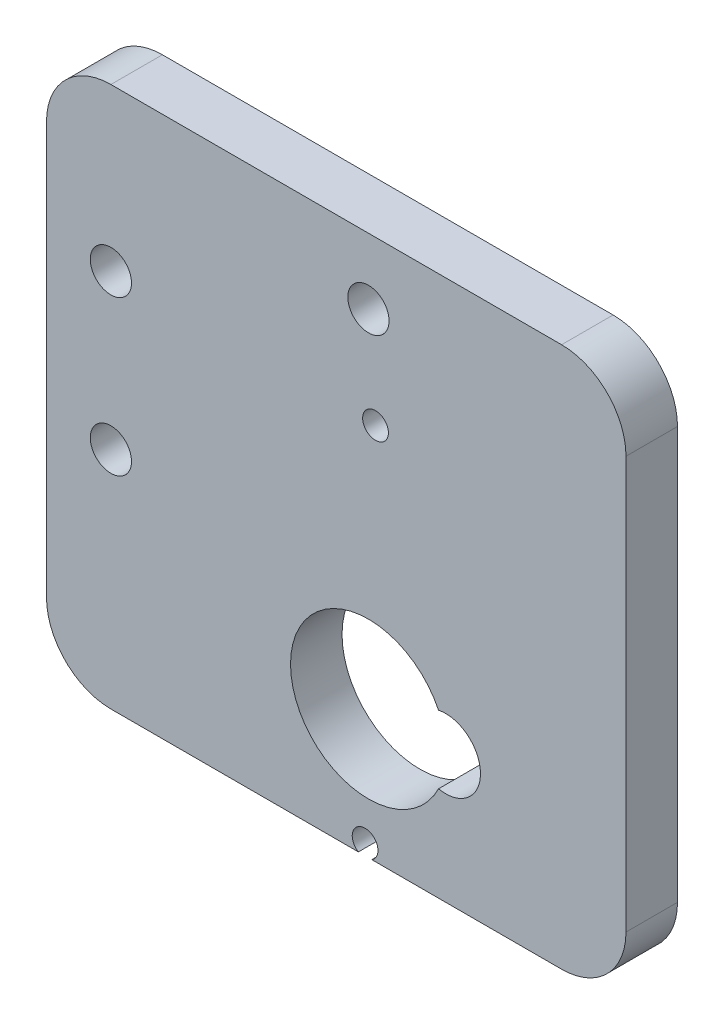
SolidWorks part; units mm, degrees
ref_plane "Front Plane" through (0, 0, 0) normal (0, 0, 1) x (1, 0, 0)
ref_plane "Top Plane" through (0, 0, 0) normal (0, 1, 0) x (1, 0, 0)
ref_plane "Right Plane" through (0, 0, 0) normal (1, 0, 0) x (0, 0, -1)
sketch "Sketch1" plane through (0, 0, 0) normal (0, 0, 1) x (1, 0, 0)
  line L0 (0, 0) -> (0, 26.9) construction
  line L1 (0, 13.45) -> (-20, 13.45) construction
  line L2 (-25, 32) -> (20, 32)
  line L3 (-25, 32) -> (-25, -10)
  line L4 (-25, -10) -> (20, -10)
  line L5 (20, 32) -> (20, -10)
  line L6 (-20, 19.45) -> (-20, 7.45) construction
  arc A0 (5.4427, 2.6419) -> (5.4427, -2.6419) centre (0, 0) ccw
  arc A1 (5.4427, -2.6419) -> (5.4427, 2.6419) centre (6, 0) ccw
  circle A2 centre (0, 26.9) radius 1.6
  circle A3 centre (-20, 19.45) radius 1.6
  circle A4 centre (-20, 7.45) radius 1.6
  arc A5 (0.3168, -9.963) -> (-0.8827, -9.9289) centre (-0.2602, -9.1463) ccw construction
  arc A6 (0.3168, -9.963) -> (-0.8827, -9.9289) centre (-0.2602, -9.1463) ccw
  arc A7 (0.3168, -9.963) -> (-0.8827, -9.9289) centre (-0.2602, -9.1463) cw
  arc A8 (-0.0268, 20.1589) -> (1.1727, 20.1248) centre (0.5502, 19.3422) ccw construction
  arc A9 (-0.0268, 20.1589) -> (1.1727, 20.1248) centre (0.5502, 19.3422) ccw
  arc A10 (-0.0268, 20.1589) -> (1.2511, 18.629) centre (0.5502, 19.3422) cw
  dimension "D1" = 12.1
  dimension "D3" = 5.4
  dimension "D9" = 3.2
  dimension "D2" = 6
  dimension "D4" = 26.9
  dimension "D5" = 45
  dimension "D6" = 14
  dimension "D7" = 42
  dimension "D8" = 10
  dimension "D10" = 12
  dimension "D11" = 20
extrude "Boss-Extrude1" add sketch "Sketch1" along normal blind 4 contours A9 L5 L2 L3 L4 A4 A3 A2 A1 A0 A6 A7
fillet "Fillet1" radius 5 4 edges at (20, 32, 2) (20, -10, 2) (-25, -10, 2) (-25, 32, 2)
